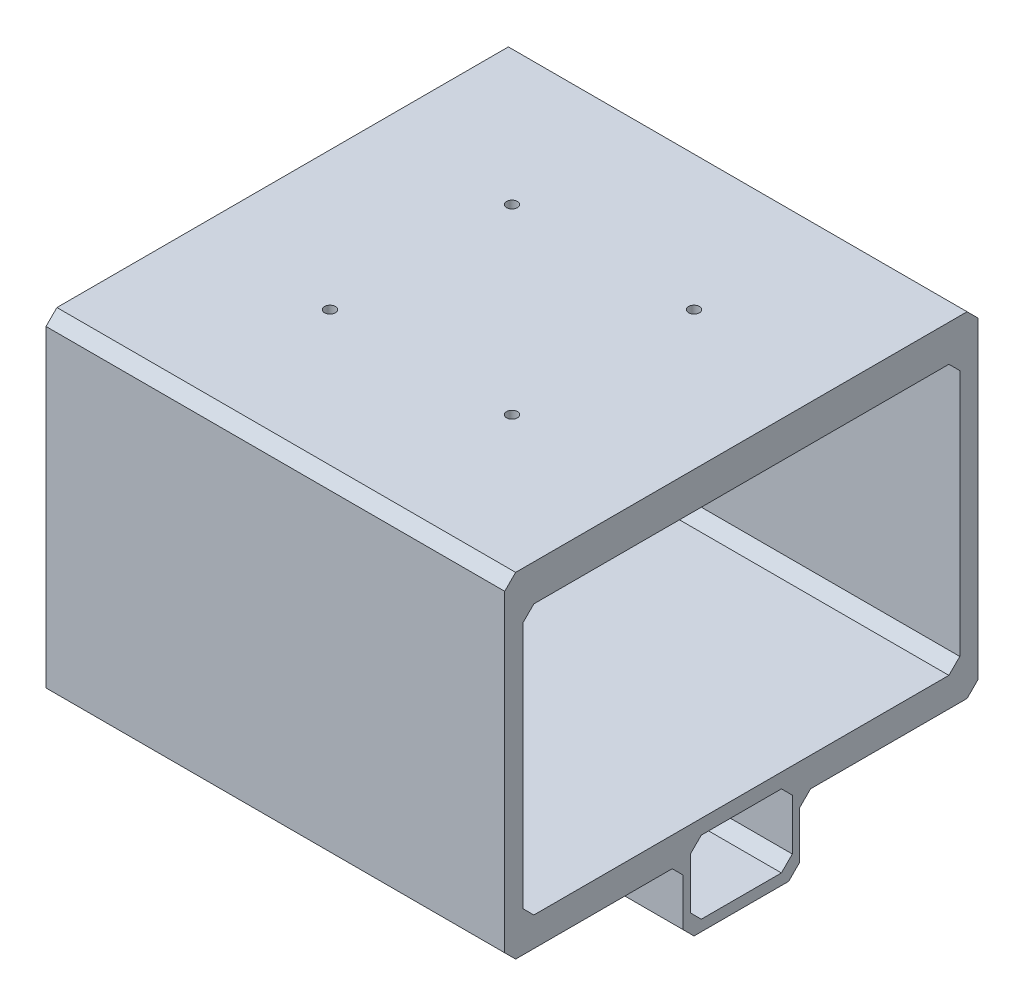
SolidWorks part; units mm, degrees
ref_plane "Front Plane" through (0, 0, 0) normal (0, 0, 1) x (1, 0, 0)
ref_plane "Top Plane" through (0, 0, 0) normal (0, 1, 0) x (1, 0, 0)
ref_plane "Right Plane" through (0, 0, 0) normal (1, 0, 0) x (0, 0, -1)
sketch "Sketch1" plane through (0, 0, 0) normal (0, 1, 0) x (1, 0, 0)
  line L0 (38, -40) -> (88, -40) construction
  line L1 (0, 0) -> (126, 0)
  line L2 (0, 0) -> (0, -130)
  line L3 (0, -130) -> (126, -130)
  line L4 (126, 0) -> (126, -130)
  line L5 (88, -40) -> (88, -90) construction
  line L6 (88, -90) -> (38, -90) construction
  line L7 (38, -90) -> (38, -40) construction
  line L8 (63, -40) -> (63, -90) construction
  line L9 (88, -65) -> (38, -65) construction
  circle A0 centre (38, -40) radius 1.5
  circle A1 centre (88, -40) radius 1.5
  circle A2 centre (88, -90) radius 1.5
  circle A3 centre (38, -90) radius 1.5
  point P17 (85.6797, -84.7539)
  dimension "D3" = 3
  dimension "D5" = 50
  dimension "D4" = 50
  dimension "D8" = 126
  dimension "D9" = 130
  dimension "D1" = 2
  dimension "D2" = 2
extrude "Boss-Extrude1" add sketch "Sketch1" along normal blind 10
sketch "Sketch3" plane through (0, 0, 0) normal (0, -1, 0) x (1, 0, 0)
  line L0 (0, 0) -> (0, 130) construction
  line L1 (126, 130) -> (0, 130)
  line L2 (126, 130) -> (126, 125)
  line L3 (126, 125) -> (0, 125)
  line L4 (0, 130) -> (0, 125)
  line L6 (126, 0) -> (0, 0)
  line L7 (126, 0) -> (126, 5)
  line L8 (126, 5) -> (0, 5)
  line L9 (0, 0) -> (0, 5)
  dimension "D1" = 5
extrude "Boss-Extrude2" add sketch "Sketch3" along normal blind 82
sketch "Sketch4" plane through (126, 0, 0) normal (1, 0, 0) x (0, 0, -1)
  line L0 (0, 10) -> (0, -82) construction
  line L1 (-130, -82) -> (0, -82)
  line L2 (-130, -82) -> (-130, -74)
  line L3 (-130, -74) -> (0, -74)
  line L4 (0, -82) -> (0, -74)
  line L5 (-65, -82) -> (-65, -74) construction
  line L8 (-79, -78) -> (-51, -78)
  line L17 (-51, -78) -> (-51, -98)
  line L18 (-51, -98) -> (-79, -98)
  line L19 (-79, -98) -> (-79, -78)
  line L20 (-81, -76) -> (-81, -101)
  line L21 (-81, -101) -> (-49, -101)
  line L22 (-49, -101) -> (-49, -76)
  line L23 (-49, -76) -> (-81, -76)
  point P15 (-49, -92.4734)
  point P18 (-65, -70)
  point P19 (0, 0)
  point P20 (0, 0)
  point P21 (-51, -70)
  point P22 (-49, -74.534)
  point P23 (-79, -79.5728)
  point P24 (-51, -81.1463)
  line M9 (-125, -82) -> (-125, 0)
  line M11 (-5, 0) -> (-5, -82)
  dimension "D2" = 32
  dimension "D3" = 28
  dimension "D1" = 8
  dimension "D4" = 2
  dimension "D5" = 25
  dimension "D6" = 20
  dimension "D7" = 2
  dimension "D8" = 2
extrude "Boss-Extrude4" add sketch "Sketch4" against normal up to surface (126 mm away) contours L23 L5 L3 L1 L20 M9 | L8 L5 L23 L20 L1 L19 | L21 L22 L1 L17 L18 L19 L20 | L5 L8 L17 L1 L22 L23 | L5 L23 L22 L1 L3 M11 up to face at (0, -38.5, 65)
sketch "Sketch5" plane through (0, -101, 0) normal (0, -1, 0) x (1, 0, 0)
  line L0 (0, 49) -> (0, 81) construction
  line L1 (126, 81) -> (126, 49) construction
  line L2 (0, 81) -> (126, 81) construction
  circle A0 centre (25, 65) radius 1.5
  circle A1 centre (63, 65) radius 1.5
  circle A2 centre (101, 65) radius 1.5
  dimension "D2" = 3
  dimension "D3" = 25
  dimension "D4" = 16
  dimension "D5" = 25
  dimension "D1" = 3
extrude "Cut-Extrude1" cut sketch "Sketch5" against normal up to surface (3 mm away) up to face at (63, -98, 65)
sketch "Sketch6" plane through (0, 0, 81) normal (0, 0, 1) x (1, 0, 0)
  line L0 (126, -82) -> (126, -101) construction
  line L1 (0, -101) -> (0, -82) construction
  line L2 (0, -101) -> (126, -101) construction
  circle A0 centre (106, -91) radius 1.5
  circle A1 centre (63, -91) radius 1.5
  circle A2 centre (20, -91) radius 1.5
  dimension "D2" = 3
  dimension "D4" = 20
  dimension "D5" = 10
  dimension "D3" = 20
  dimension "D1" = 3
extrude "Cut-Extrude2" cut sketch "Sketch6" against normal up to surface (2 mm away) up to face at (63, -88, 79)
chamfer "Chamfer1" distance 3 angle 45 16 edges at (63, -74, 125) (63, 0, 125) (63, 0, 5) (63, -74, 5) (63, -98, 51) (63, -98, 79) (63, -78, 51) (63, -78, 79) (63, -82, 81) (63, -82, 49) (63, -101, 49) (63, -101, 81) (63, -82, 0) (63, -82, 130) (63, 10, 130) (63, 10, 0)
